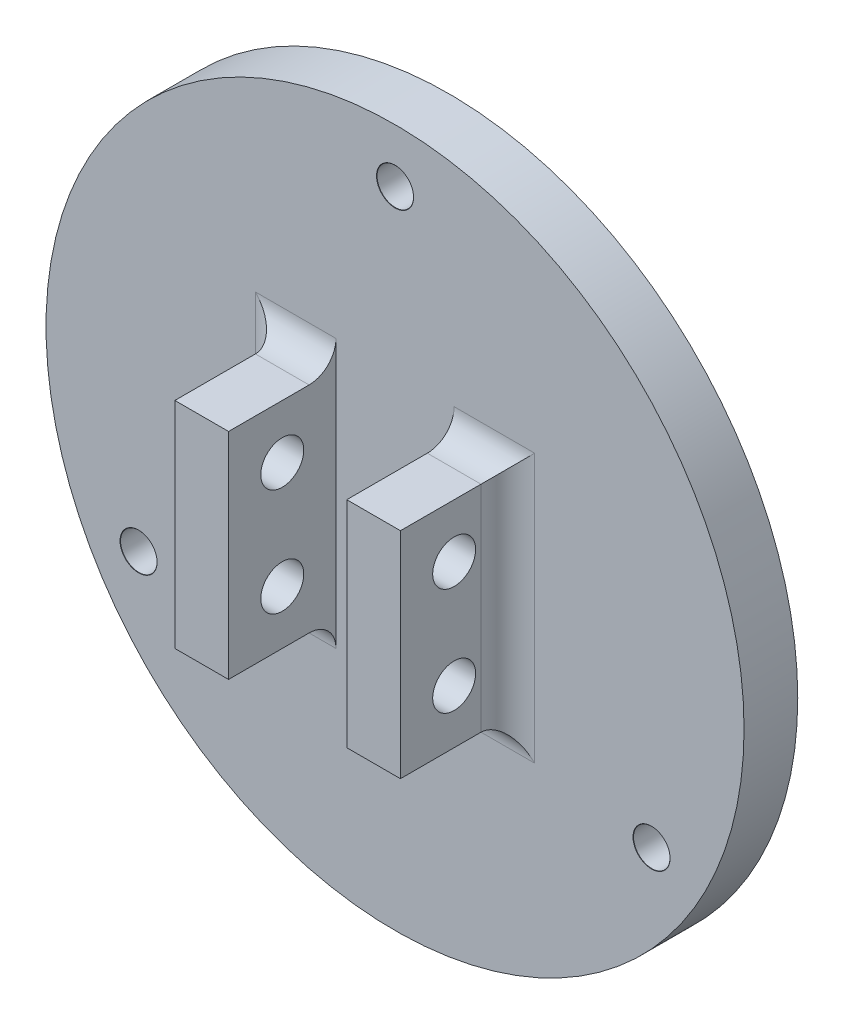
SolidWorks part; units mm, degrees
material "7075-T6 (SN)"
ref_plane "정면" through (0, 0, 0) normal (0, 0, 1) x (1, 0, 0)
ref_plane "윗면" through (0, 0, 0) normal (0, 1, 0) x (1, 0, 0)
ref_plane "우측면" through (0, 0, 0) normal (1, 0, 0) x (0, 0, -1)
sketch "스케치1" plane through (0, 0, 0) normal (0, 0, 1) x (1, 0, 0)
  circle A0 centre (0, 0) radius 32.5
  dimension "D1" = 65
extrude "보스-돌출1" add sketch "스케치1" along normal blind 5
sketch "스케치2" plane through (0, 0, 5) normal (0, 0, 1) x (1, 0, 0)
hole_wizard "M3 여유 구멍1" positions "스케치3" profile "스케치4" hole size "M3" standard "ISO"
sketch "스케치3" plane through (0, 0, 5) normal (0, 0, 1) x (1, 0, 0)
  circle A1 centre (0, 0) radius 27.5 construction
  circle A2 centre (0, 0) radius 32.5 construction
  point P0 (0, 27.5)
  point P9 (0, 0)
  dimension "D1" = 55
sketch "스케치4" plane through (0, 27.5, 5) normal (1, 0, 0) x (0, -1, 0)
  line L0 (0, 0) -> (0, 6.0215)
  line L1 (0, 6.0215) -> (1.7, 5)
  line L2 (1.7, 5) -> (1.7, 0.021)
  line L3 (1.7, 0.021) -> (1.725, 0)
  line L5 (1.725, 0) -> (0, 0)
  line L6 (-1.7, 0.021) -> (-1.725, 0) construction
  line L10 (0, 6.0215) -> (-1.7, 5) construction
  line L11 (0, -6.35) -> (0, 107.95) construction
  dimension "구멍 지름" = 3.4
  dimension "구멍 깊이" = 5
  dimension "표면 카운터싱크 지름" = 3.45
  dimension "표면 카운터싱크 각도" = 100
  dimension "드릴 각도" = 118
pattern_circular "원형 패턴1" count 3 over 360 about axis through (0, -0.0777, 0) along (0, 0, 1) of "M3 여유 구멍1"
sketch "스케치5" plane through (0, 0, 5) normal (0, 0, 1) x (1, 0, 0)
  line L0 (0, 12.5377) -> (0, -12.4853) construction
  line L1 (-10.5033, -10) -> (-5.5033, -10)
  line L2 (-10.5033, -10) -> (-10.5033, 10)
  line L3 (-10.5033, 10) -> (-5.5033, 10)
  line L4 (-5.5033, -10) -> (-5.5033, 10)
  line L5 (10.5033, -10) -> (5.5033, -10)
  line L6 (10.5033, -10) -> (10.5033, 10)
  line L7 (5.5033, -10) -> (5.5033, 10)
  line L8 (10.5033, 10) -> (5.5033, 10)
  dimension "D1" = 5.5033
  dimension "D2" = 20
  dimension "D3" = 5
  dimension "D4" = 10
extrude "보스-돌출2" add sketch "스케치5" along normal blind 10
hole_wizard "M3 육각 소켓 머리 캡 나사용 카운터보어1" positions "스케치7" profile "스케치9" counterbore size "M3" standard "ISO" end condition through all
sketch "스케치7" plane through (0, 0, 0) normal (0, 0, -1) x (-1, 0, 0)
  point P0 (0, 0)
sketch "스케치9" plane through (0, 0, 0) normal (1, 0, 0) x (0, 1, 0)
  line L0 (0, 0) -> (0, 15)
  line L1 (0, 15) -> (1.7, 15)
  line L3 (1.7, 15) -> (1.7, 3.4)
  line L4 (1.7, 3.4) -> (3.25, 3.4)
  line L5 (3.25, 3.4) -> (3.25, 0)
  line L7 (3.25, 0) -> (0, 0)
  line L11 (0, -6.35) -> (0, 107.95) construction
  dimension "관통 구멍 지름" = 3.4
  dimension "관통 구멍 깊이" = 15
  dimension "카운터보어 지름" = 6.5
  dimension "카운터보어 깊이" = 3.4
sketch "스케치11" plane through (-10.5033, 0, 0) normal (-1, 0, 0) x (0, 0, 1)
  line L0 (10, 5) -> (10, -5) construction
  line L1 (5, 10) -> (5, -10) construction
  dimension "D1" = 10
  dimension "D2" = 5
  dimension "D3" = 5
hole_wizard "Ø4.0mm 맞춤핀 구멍1" positions "스케치12" profile "스케치13" hole size "Ø4.0" standard "ISO" end condition through all
sketch "스케치12" plane through (-10.5033, 0, 0) normal (-1, 0, 0) x (0, 0, 1)
  point P0 (10, 5)
  point P3 (10, -5)
sketch "스케치13" plane through (-10.5033, 5, 10) normal (0, 1, 0) x (0, 0, 1)
  line L0 (0, 0) -> (0, 43.0033)
  line L1 (0, 43.0033) -> (2, 43.0033)
  line L2 (2, 43.0033) -> (2, 0)
  line L5 (2, 0) -> (0, 0)
  line L11 (0, -6.35) -> (0, 107.95) construction
  dimension "관통 구멍 지름" = 4
  dimension "관통 구멍 깊이" = 43.0033
fillet "필렛1" radius 2.5 2 edges at (10.5033, 0, 5) (-10.5033, 0, 5)
fillet "필렛2" radius 2.5 4 edges at (9.2533, -10, 5) (-9.2533, -10, 5) (9.2533, 10, 5) (-9.2533, 10, 5)
